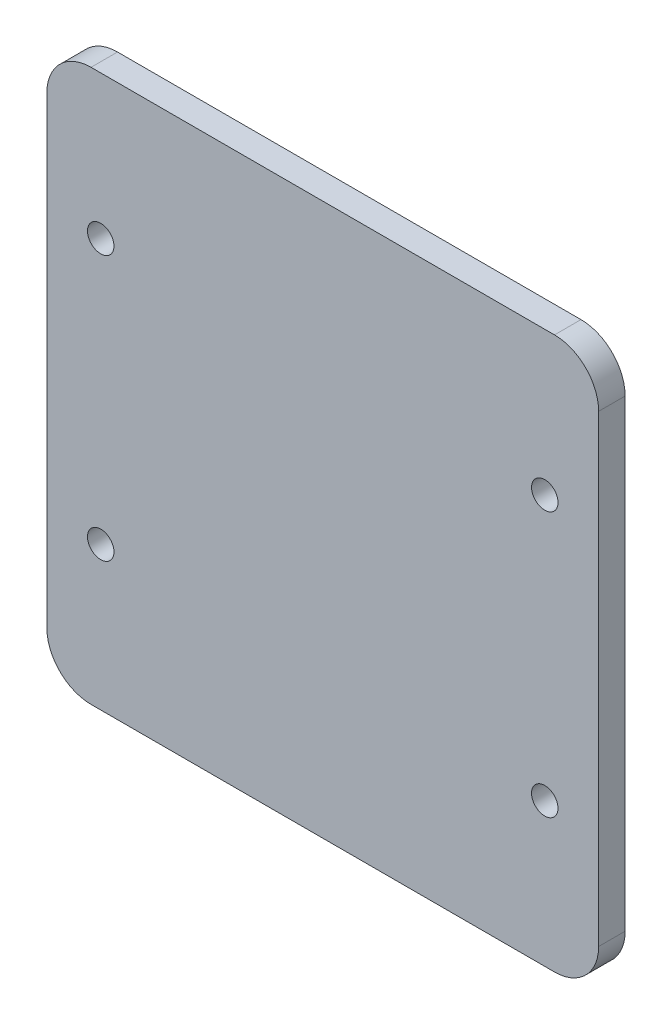
SolidWorks part; units mm, degrees
material "6061-T6 (SS)"
ref_plane "Front Plane" through (0, 0, 0) normal (0, 0, 1) x (1, 0, 0)
ref_plane "Top Plane" through (0, 0, 0) normal (0, 1, 0) x (1, 0, 0)
ref_plane "Right Plane" through (0, 0, 0) normal (1, 0, 0) x (0, 0, -1)
sketch "Sketch1" plane through (0, 0, 0) normal (0, 0, 1) x (1, 0, 0)
  line L1 (62.5, -62.5) -> (-62.5, -62.5)
  line L2 (62.5, -62.5) -> (62.5, 62.5)
  line L3 (62.5, 62.5) -> (-62.5, 62.5)
  line L4 (-62.5, -62.5) -> (-62.5, 62.5)
  line L5 (62.5, -62.5) -> (-62.5, 62.5) construction
  line L6 (62.5, 62.5) -> (-62.5, -62.5) construction
  point P0 (0, 0)
  dimension "D1" = 125
extrude "Boss-Extrude1" add sketch "Sketch1" along normal blind 6
fillet "Fillet1" radius 10 4 edges at (-62.5, 62.5, 3) (62.5, 62.5, 3) (62.5, -62.5, 3) (-62.5, -62.5, 3)
sketch "Sketch9" plane through (0, 0, 6) normal (0, 0, 1) x (1, 0, 0)
  circle A0 centre (50.3, 30) radius 3
  circle A1 centre (50.3, -30) radius 3
  circle A2 centre (-50.3, 30) radius 3
  circle A3 centre (-50.3, -30) radius 3
extrude "Cut-Extrude1" cut sketch "Sketch9" against normal blind 10
